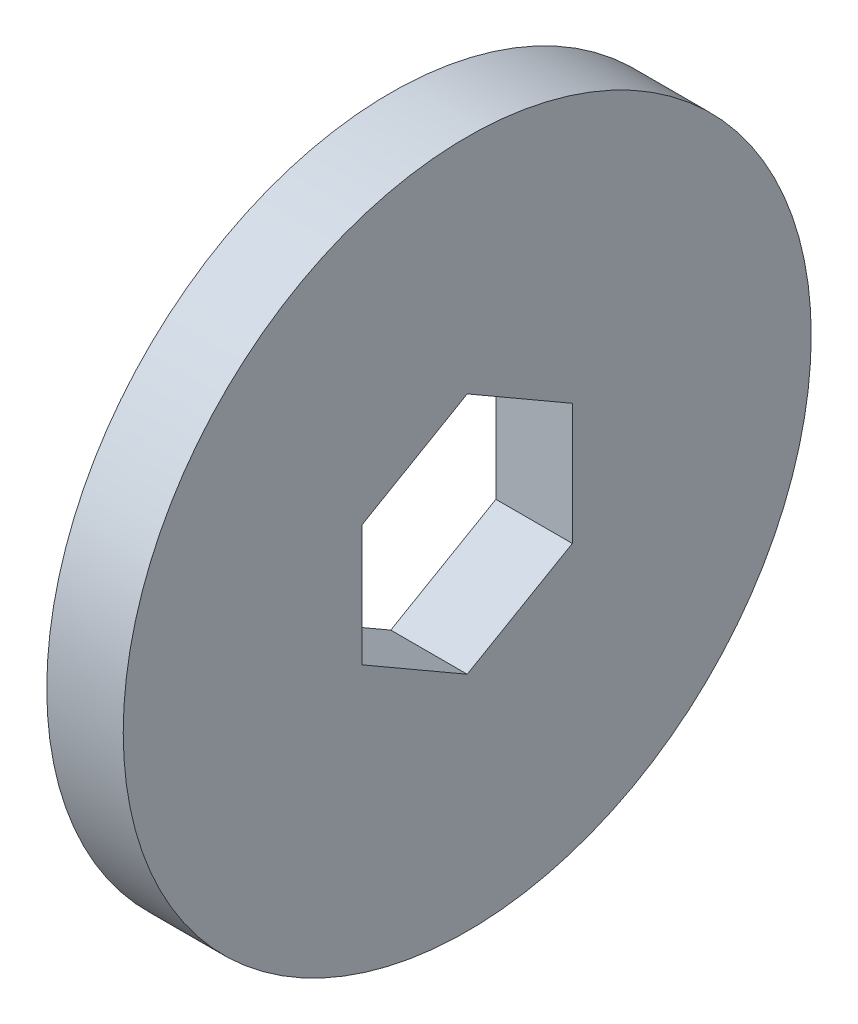
SolidWorks part; units mm, degrees
material "Pine"
ref_plane "Front Plane" through (0, 0, 0) normal (0, 0, 1) x (1, 0, 0)
ref_plane "Top Plane" through (0, 0, 0) normal (0, 1, 0) x (1, 0, 0)
ref_plane "Right Plane" through (0, 0, 0) normal (1, 0, 0) x (0, 0, -1)
sketch "Sketch1" plane through (0, 0, 0) normal (1, 0, 0) x (0, 0, -1)
  circle A0 centre (0, 0) radius 9
  dimension "D1" = 18
extrude "Boss-Extrude1" add sketch "Sketch1" along normal blind 2
sketch "Sketch2" plane through (2, 0, 0) normal (1, 0, 0) x (0, 0, -1)
  line L1 (0, 3.1754) -> (-2.75, 1.5877)
  line L2 (-2.75, 1.5877) -> (-2.75, -1.5877)
  line L3 (-2.75, -1.5877) -> (0, -3.1754)
  line L4 (0, -3.1754) -> (2.75, -1.5877)
  line L5 (2.75, -1.5877) -> (2.75, 1.5877)
  line L6 (2.75, 1.5877) -> (0, 3.1754)
  circle A2 centre (0, 0) radius 2.75 construction
  dimension "D1" = 5.5
extrude "Cut-Extrude1" cut sketch "Sketch2" against normal through all
